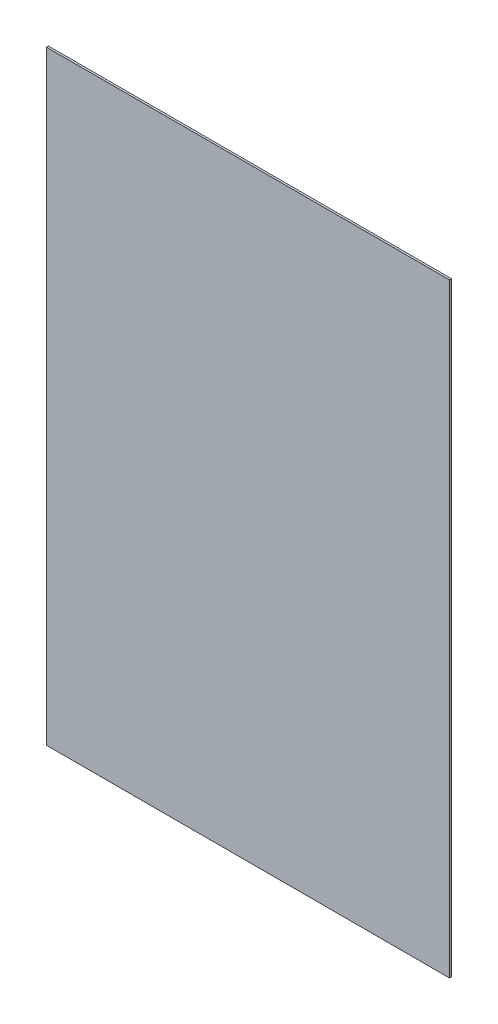
SolidWorks part; units mm, degrees
ref_plane "Plan de face" through (0, 0, 0) normal (0, 0, 1) x (1, 0, 0)
ref_plane "Plan de dessus" through (0, 0, 0) normal (0, 1, 0) x (1, 0, 0)
ref_plane "Plan de droite" through (0, 0, 0) normal (1, 0, 0) x (0, 0, -1)
sketch "Esquisse1" plane through (0, 0, 0) normal (0, 0, 1) x (1, 0, 0)
  line L1 (0, 0) -> (2000, 0)
  line L2 (0, 0) -> (0, 3000)
  line L3 (0, 3000) -> (2000, 3000)
  line L4 (2000, 0) -> (2000, 3000)
  dimension "D1" = 3000
  dimension "D2" = 2000
extrude "Boss.-Extru.1" add sketch "Esquisse1" along normal blind 10
